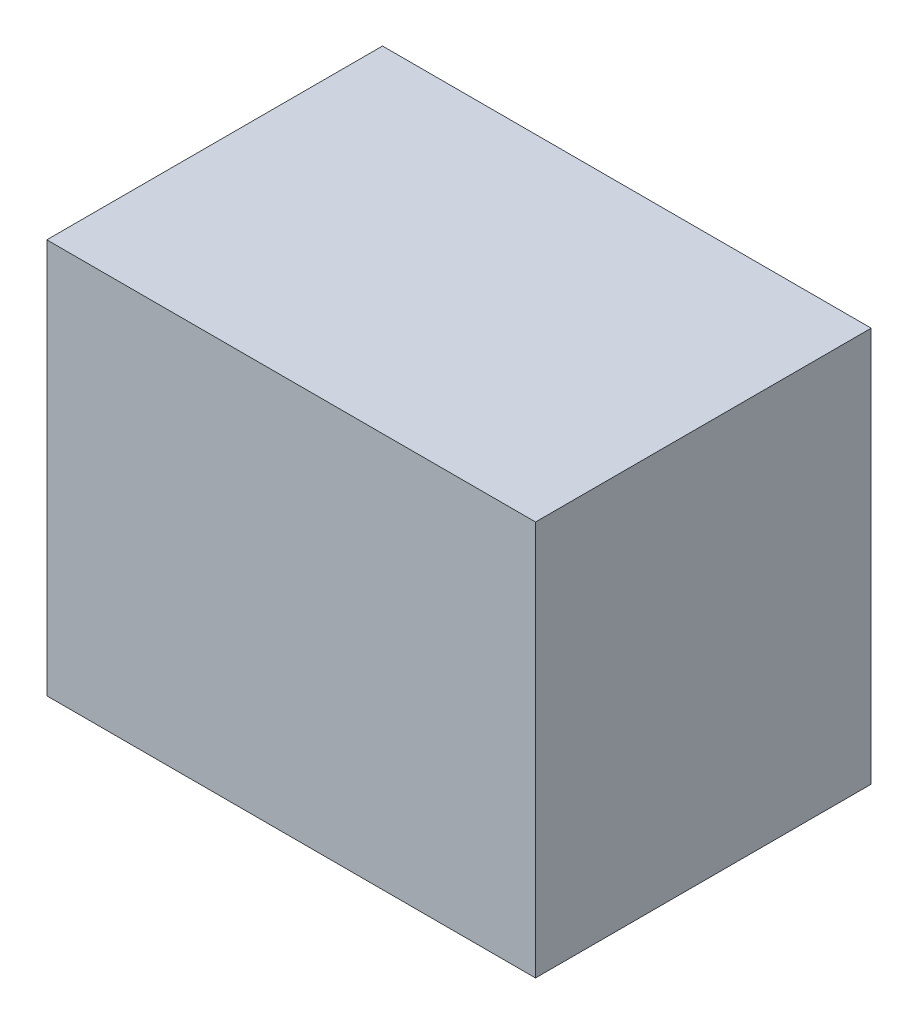
SolidWorks part; units mm, degrees
ref_plane "Front Plane" through (0, 0, 0) normal (0, 0, 1) x (1, 0, 0)
ref_plane "Top Plane" through (0, 0, 0) normal (0, 1, 0) x (1, 0, 0)
ref_plane "Right Plane" through (0, 0, 0) normal (1, 0, 0) x (0, 0, -1)
sketch "Sketch1" plane through (0, 0, 0) normal (1, 0, 0) x (0, 0, -1)
  line L1 (170, -200) -> (-170, -200)
  line L2 (170, -200) -> (170, 200)
  line L3 (170, 200) -> (-170, 200)
  line L4 (-170, -200) -> (-170, 200)
  line L5 (170, -200) -> (-170, 200) construction
  line L6 (170, 200) -> (-170, -200) construction
  point P0 (0, 0)
  dimension "D1" = 340
  dimension "D2" = 400
extrude "Boss-Extrude1" add sketch "Sketch1" along normal blind 495
